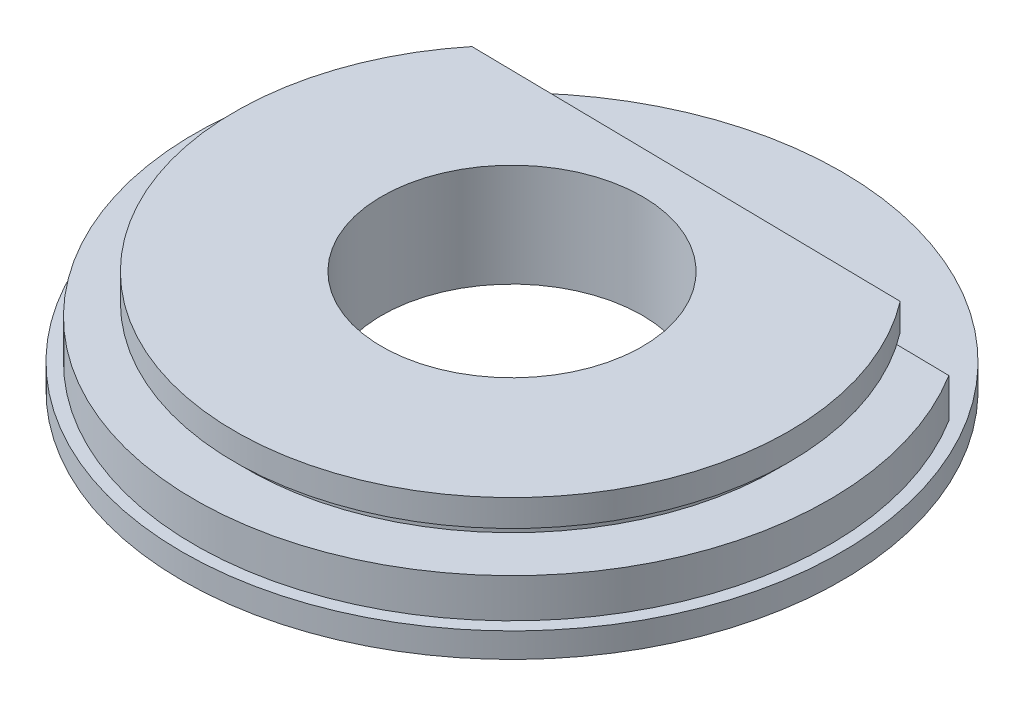
SolidWorks part; units mm, degrees
ref_plane "Front Plane" through (0, 0, 0) normal (0, 0, 1) x (1, 0, 0)
ref_plane "Top Plane" through (0, 0, 0) normal (0, 1, 0) x (1, 0, 0)
ref_plane "Right Plane" through (0, 0, 0) normal (1, 0, 0) x (0, 0, -1)
sketch "Sketch1" plane through (0, 0, 0) normal (0, 0, 1) x (1, 0, 0)
  line L0 (15.8026, 0) -> (40, 0)
  line L1 (40, 0) -> (40, 3)
  line L2 (40, 3) -> (38.5, 3)
  line L3 (38.5, 3) -> (38.5, 7.75)
  line L4 (38.5, 7.75) -> (32.1135, 7.75)
  line L5 (32.1135, 7.75) -> (32.1135, 9.25)
  line L6 (32.1135, 9.25) -> (33.6135, 9.25)
  line L7 (33.6135, 9.25) -> (33.6135, 12.5)
  line L8 (33.6135, 12.5) -> (15.8026, 12.5)
  line L9 (15.8026, 12.5) -> (15.8026, 0)
  line L10 (0, 0) -> (0, 24.3391) construction
  dimension "D1" = 3
  dimension "D2" = 1.5
  dimension "D3" = 4.75
  dimension "D4" = 1.5
  dimension "D5" = 1.5
  dimension "D6" = 12.5
revolve "Revolve1" add sketch "Sketch1" angle 360 about L10
sketch "Sketch2" plane through (0, 12.5, 0) normal (0, 1, 0) x (1, 0, 0)
  line L0 (-32.0672, 21.3059) -> (32.6966, 20.3269)
  circle A0 centre (0, 0) radius 38.5 construction
  arc A2 (32.6966, 20.3269) -> (-32.0672, 21.3059) centre (0, 0) ccw
extrude "Cut-Extrude1" cut sketch "Sketch2" against normal up to surface (9.5 mm away) up to face at (0, 3, -38.5)
